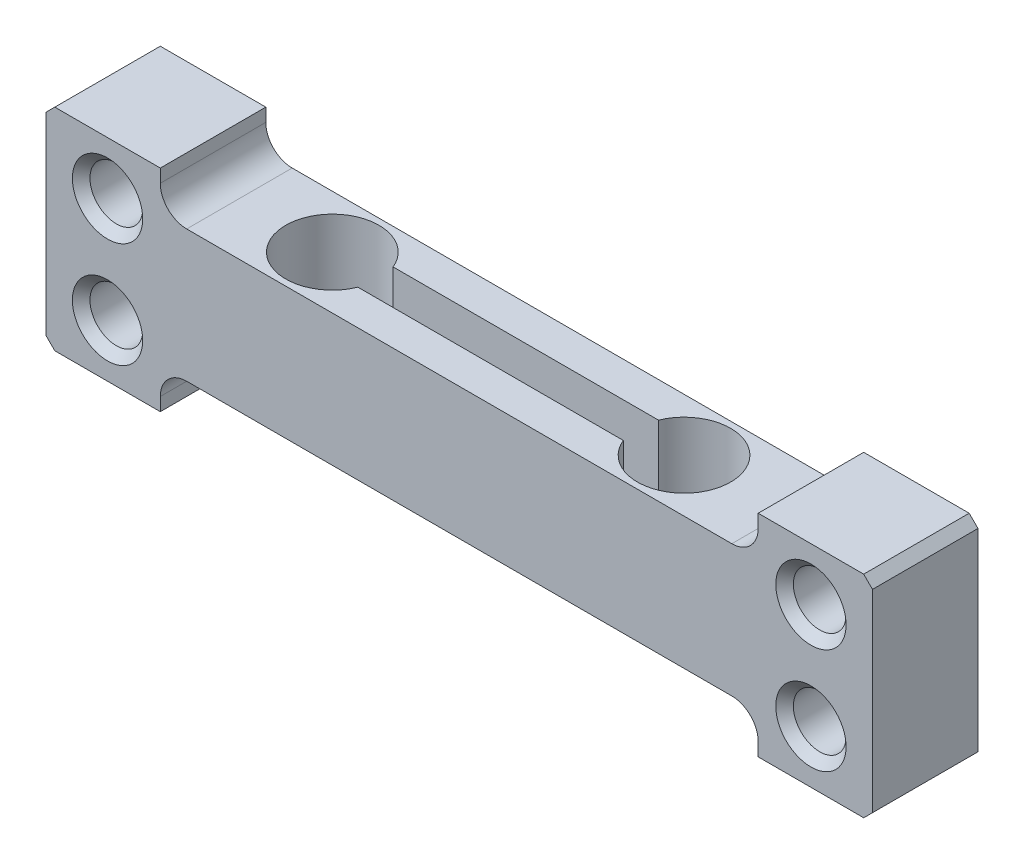
SolidWorks part; units mm, degrees
other "细节项目1"
ref_plane "Front" through (0, 0, 0) normal (0, 0, 1) x (1, 0, 0)
ref_plane "Top" through (0, 0, 0) normal (0, 1, 0) x (1, 0, 0)
ref_plane "Right" through (0, 0, 0) normal (1, 0, 0) x (0, 0, -1)
sketch "草图1" plane through (0, 0, 0) normal (0, 0, 1) x (1, 0, 0)
  line L0 (40.5, 11.25) -> (40.5, 12)
  line L1 (0, 0) -> (6.5, 0)
  line L2 (0, 0) -> (0, 12)
  line L3 (0, 12) -> (6.5, 12)
  line L4 (47, 0) -> (47, 12)
  line L5 (8, 9.75) -> (39, 9.75)
  line L6 (6.5, 0) -> (6.5, 0.75)
  line L7 (40.5, 0) -> (40.5, 0.75)
  line L8 (40.5, 12) -> (47, 12)
  line L9 (40.5, 0) -> (47, 0)
  line L10 (0, 12) -> (47, 12) construction
  line L11 (8, 2.25) -> (39, 2.25)
  line L12 (0, 9.75) -> (47, 9.75) construction
  line L13 (6.5, 11.25) -> (6.5, 12)
  line L14 (40.5, 0) -> (40.5, 12) construction
  line L16 (6.5, 0) -> (6.5, 12) construction
  circle A0 centre (3.5, 3) radius 1.5
  circle A1 centre (3.5, 9) radius 1.5
  circle A2 centre (43.5, 3) radius 1.5
  circle A3 centre (43.5, 9) radius 1.5
  arc A4 (8, 9.75) -> (6.5, 11.25) centre (8, 11.25) cw
  arc A5 (40.5, 11.25) -> (39, 9.75) centre (39, 11.25) cw
  arc A6 (40.5, 0.75) -> (39, 2.25) centre (39, 0.75) ccw
  arc A7 (6.5, 0.75) -> (8, 2.25) centre (8, 0.75) cw
  point P15 (0, 2.25)
  point P16 (47, 2.25)
  point P29 (6.5, 9.75)
  point P32 (40.5, 9.75)
  dimension "D1" = 3.5
  dimension "D2" = 3
  dimension "D3" = 3
  dimension "D4" = 3.5
  dimension "D5" = 1.5
  dimension "D9" = 1.5
  dimension "D10" = 1.5
  dimension "D11" = 1.5
  dimension "D6" = 2.25
  dimension "D7" = 6.5
  dimension "D8" = 6.5
extrude "凸台-拉伸1" add sketch "草图1" along normal blind 6
chamfer "倒角1" distance 0.5 angle 45 4 edges at (0, 0, 3) (0, 12, 3) (47, 0, 3) (47, 12, 3)
sketch "草图2" plane through (0, 9.75, 0) normal (0, 1, 0) x (1, 0, 0)
  line L0 (39, -6) -> (8, -6) construction
  line L2 (30.8295, -2) -> (15.7376, -2)
  line L3 (30.8295, -4) -> (15.7376, -4)
  arc A0 (30.8295, -4) -> (30.8295, -2) centre (33.2836, -3) ccw
  arc A2 (15.7376, -2) -> (15.7376, -4) centre (13.2836, -3) ccw
  point P9 (31.0662, -4)
  point P10 (14.9726, -4)
  point P12 (14.9726, -2)
  point P13 (31.3603, -2)
  dimension "D1" = 3
  dimension "D2" = 20
extrude "切除-拉伸1" cut sketch "草图2" against normal blind 10
chamfer "倒角2" distance 0.5 angle 45 8 edges at (5, 3, 6) (5, 9, 6) (5, 3, 0) (5, 9, 0) (45, 3, 0) (45, 9, 0) (45, 9, 6) (45, 3, 6)
